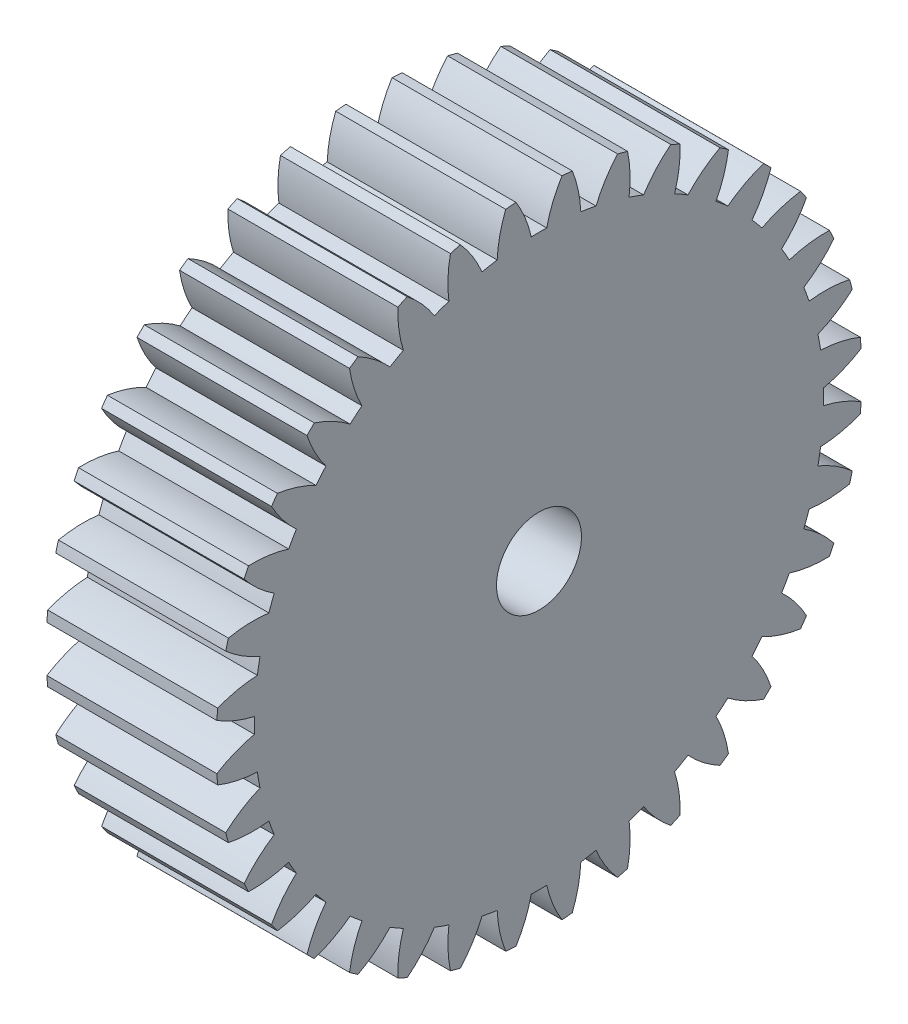
SolidWorks part; units mm, degrees
ref_plane "Plane1" through (0, 0, 0) normal (0, 0, 1) x (1, 0, 0)
ref_plane "Plane2" through (0, 0, 0) normal (0, 1, 0) x (1, 0, 0)
ref_plane "Plane3" through (0, 0, 0) normal (1, 0, 0) x (0, 0, -1)
other "Configuration Table"
sketch "HoldingSke" plane through (0, 0, 0) normal (0, 1, 0) x (1, 0, 0)
  line L0 (0, 0) -> (0.809, -0.5878)
  line L1 (-15, 0) -> (100, 0) construction
  line L2 (0, 0) -> (-2.1039, 2.3779)
  line L3 (0, 0) -> (-11.863, 4.5341)
  line L4 (0, 0) -> (6.9867, 5.0761)
  line L5 (0, 0) -> (-46.8476, -17.4728)
  line L6 (0, 0) -> (-8.2896, -5.593)
  line L7 (-2.1039, 2.3779) -> (8.6586, 51.2059)
  line L8 (-76.2, 54.61) -> (-75.3, 54.61)
  line L9 (-71.009, 38.7566) -> (-53.1078, 45.2721)
  line L10 (-76.2, 71.12) -> (104.1128, 71.12)
  line L11 (0, 0) -> (-10, 0)
  line L12 (-76.2, 101.6) -> (-76.162, 101.6)
  line L13 (24.9733, 27.94) -> (52.9518, 28.4284)
  line L14 (24.9733, 27.94) -> (24.9743, 27.94)
  line L15 (24.9733, 27.94) -> (100.4006, 29.5858)
  line L16 (-63.627, -1) -> (-12.827, -1)
  circle A0 centre (0, 0) radius 2.5
  circle A1 centre (0, 0) radius 16.749
  circle A2 centre (0, 0) radius 37.5
  circle A3 centre (0, 0) radius 2.5
  dimension "MHD" = 33.498
  dimension "Hub_dia" = 75
  dimension "Bore" = 5
  dimension "MBD" = 5
  dimension "Num_teeth" = 36
  dimension "Pitch" = 1
  dimension "Overall_len" = 50
  dimension "Show_teeth" = 36
  dimension "Thickness" = 10
  dimension "OAL" = 50.0001
  dimension "T_dim" = 0.9
  dimension "Ap" = 20
  dimension "H" = 19.05
  dimension "Pitch_radius" = 180.3128
  dimension "Width" = 10
  dimension "Backlash" = 0.038
  dimension "Addendum_fac" = 1
  dimension "Dedendum_fac" = 1.25
  dimension "Clearance_fac" = 0.25
  dimension "Dedendum_add" = 0.001
  dimension "Module" = 1
sketch "BasProSke" plane through (0, 0, 0) normal (0, 1, 0) x (1, 0, 0)
  line L0 (-10, 0) -> (60, 0) construction
  line L1 (0, 0) -> (0, 19)
  line L2 (0, 0) -> (10, 0)
  line L3 (10, 0) -> (10, 19)
  line L4 (10, 19) -> (0, 19)
  dimension "Thickness" = 10
  dimension "Diameter" = 38
revolve "Base-Revolve" add sketch "BasProSke" angle 360 about L0
sketch "TooCutSke" plane through (0, 0, 0) normal (1, 0, 0) x (0, 0, -1)
  line L1 (0, 0) -> (0, 107) construction
  line L2 (0, 0) -> (-0.8516, 17.9798) construction
  line L3 (0, 0) -> (-3.1351, 35.8344) construction
  line L4 (-0.8516, 17.9798) -> (-1.5676, 17.9172) construction
  arc A0 (0.4547, 16.7428) -> (-0.4547, 16.7428) centre (0, 0) ccw
  arc A1 (1.3689, 18.9761) -> (-1.3689, 18.9761) centre (0, 0) ccw
  circle A2 centre (0, 0) radius 18 construction
  circle A3 centre (0, 0) radius 16.9145 construction
  arc A4 (-0.4547, 16.7428) -> (-1.3689, 18.9761) centre (-7.4808, 15.1702) ccw
  arc A5 (1.3689, 18.9761) -> (0.4547, 16.7428) centre (7.4808, 15.1702) ccw
  dimension "Root_dia" = 33.498
  dimension "Overcut_dia" = 38.0508
  dimension "Pitch_dia" = 36
  dimension "Base_dia" = 33.8289
  dimension "Flank_rad" = 7.2
  dimension "Half_ang" = 5
  dimension "Half_CT" = 0.7186
extrude "ToothCut" cut sketch "TooCutSke" along normal through all
fillet "Breaks" [suppressed] radius 0.02
fillet "RootFillets" [suppressed] radius 0.251
pattern_circular "TeethCuts" count 36 every 10 about axis through (-10, 0, 0) along (1, 0, 0) of "ToothCut", "RootFillets", "Breaks"
sketch "HubNeaOneSke" plane through (0, 0, 0) normal (-1, 0, 0) x (0, 0, 1)
  circle A0 centre (0, 0) radius 16.749
  dimension "Diameter" = 33.498
extrude "HubNearOne" [suppressed] add sketch "HubNeaOneSke" along normal blind 40.0001
sketch "HubNeaBotSke" plane through (0, 0, 0) normal (-1, 0, 0) x (0, 0, 1)
  circle A0 centre (0, 0) radius 16.749
  dimension "Diameter" = 33.498
extrude "HubNearBoth" [suppressed] add sketch "HubNeaBotSke" along normal blind 20
ref_plane "FarPln" through (10, 0, 0) normal (1, 0, 0) x (0, 0, -1)
sketch "HubFarSke" plane through (10, 0, 0) normal (1, 0, 0) x (0, 0, -1)
  circle A0 centre (0, 0) radius 16.749
  dimension "Diameter" = 33.498
extrude "HubFar" [suppressed] add sketch "HubFarSke" along normal blind 20
sketch "BorSke" plane through (0, 0, 0) normal (1, 0, 0) x (0, 0, -1)
  circle A0 centre (0, 0) radius 2.5
  dimension "Diameter" = 5
extrude "Bore" cut sketch "BorSke" along normal mid plane 100.0001
sketch "KeySke" plane through (0, 0, 0) normal (1, 0, 0) x (0, 0, -1)
  line L0 (-1, 0) -> (-1, 3.4)
  line L1 (-1, 3.4) -> (1, 3.4)
  line L2 (1, 3.4) -> (1, 0)
  line L3 (0, 0) -> (0, 34) construction
  line L4 (-1, 0) -> (1, 0)
  dimension "Offset" = 3.4
  dimension "Width" = 2
extrude "Keyway" [suppressed] cut sketch "KeySke" along normal mid plane 100.0001
pattern_circular "Keyway2" [suppressed] count 2 every 90 about axis through (-10, 0, 0) along (1, 0, 0)
equation "' \"Module@HoldingSke\" = 6.35"
equation "' \"Num_teeth@HoldingSke\" = 12"
equation "' \"Ap@HoldingSke\" =  20"
equation "' \"Ap@HoldingSke\" = 20"
equation "' \"Width@HoldingSke\" = 0.5 * 25.4"
equation "' \"Hub_dia@HoldingSke\"= 1 * 25.4"
equation "' \"Hub_dia@HoldingSke\" = 1 * 25.4"
equation "' \"Overall_len@HoldingSke\" = 1.0 * 25.4"
equation "' \"Bore@HoldingSke\" = 0.75 * 25.4"
equation "' \"T_dim@HoldingSke\" = 0.1 * 25.4"
equation "' \"Width@KeySke\" = 0.25 * 25.4"
equation "' \"Show_teeth@HoldingSke\" = 13"
equation "' \"Backlash@HoldingSke\" = 0.009 * 25.4"
equation "' \"Addendum_fac@HoldingSke\" = 1.0"
equation "' \"Dedendum_fac@HoldingSke\" = 1.25"
equation "' \"Dedendum_add@HoldingSke\" = 0.00005 * 25.4"
equation "' \"Clearance_fac@HoldingSke\" = 0.25"
equation "\"Pitch@HoldingSke\" = 1 / \"Module@HoldingSke\""
equation "\"Overcut_dia@TooCutSke\" = (\"Num_teeth@HoldingSke\" + 2 * \"Addendum_fac@HoldingSke\") / \"Pitch@HoldingSke\" + 0.002 * 25.4"
equation "\"Pitch_dia@TooCutSke\" = \"Num_teeth@HoldingSke\" / \"Pitch@HoldingSke\""
equation "\"Base_dia@TooCutSke\" = \"Num_teeth@HoldingSke\" / \"Pitch@HoldingSke\" * cos((\"Ap@HoldingSke\"  * 3.14159265 / 180))"
equation "\"Root_dia@TooCutSke\" = (\"Num_teeth@HoldingSke\" + 2) / \"Pitch@HoldingSke\" - 2 * (\"Addendum_fac@HoldingSke\" + \"Dedendum_fac@HoldingSke\") / \"Pitch@HoldingSke\" - \"Dedendum_add@HoldingSke\" * 2"
equation "\"Half_ang@TooCutSke\" = 180 / \"Num_teeth@HoldingSke\""
equation "\"Half_CT@TooCutSke\" = \"Num_teeth@HoldingSke\" / \"Pitch@HoldingSke\" * sin((3.14159265 / 2 / \"Num_teeth@HoldingSke\")) / 2 - 7 * \"Backlash@HoldingSke\" / 4"
equation "\"Flank_rad@TooCutSke\" = \"Num_teeth@HoldingSke\" / \"Pitch@HoldingSke\" / 5"
equation "\"Radius@RootFillets\" = \"Clearance_fac@HoldingSke\" / \"Pitch@HoldingSke\" + \"Dedendum_add@HoldingSke\""
equation "\"Break_rad@Breaks\" = 0.02 / \"Pitch@HoldingSke\""
equation "\"Thickness@HoldingSke\" = \"Width@HoldingSke\""
equation "\"OAL@HoldingSke\" = \"Thickness@HoldingSke\""
equation "\"MHD@HoldingSke\" = (\"Num_teeth@HoldingSke\" + 2) / \"Pitch@HoldingSke\" - 2 * (\"Addendum_fac@HoldingSke\" + \"Dedendum_fac@HoldingSke\")  / \"Pitch@HoldingSke\" - \"Dedendum_add@HoldingSke\" * 2"
equation "\"MBD@HoldingSke\" = (\"Num_teeth@HoldingSke\" + 2) / \"Pitch@HoldingSke\" - 2 * (\"Addendum_fac@HoldingSke\" + \"Dedendum_fac@HoldingSke\")  / \"Pitch@HoldingSke\" - \"Dedendum_add@HoldingSke\" * 2 - 0.002 * 25.4"
equation "\"MHD@HoldingSke\" = ((sgn( \"MHD@HoldingSke\" - \"Hub_dia@HoldingSke\" )-1)*( \"MHD@HoldingSke\" - \"Hub_dia@HoldingSke\" ))/-2+ \"Hub_dia@HoldingSke\""
equation "\"MBD@HoldingSke\" = ((sgn( \"MBD@HoldingSke\" - \"Bore@HoldingSke\" )-1)*( \"MBD@HoldingSke\" - \"Bore@HoldingSke\" ))/-2+ \"Bore@HoldingSke\""
equation "\"OAL@HoldingSke\" = ((sgn( \"OAL@HoldingSke\" - \"Overall_len@HoldingSke\" )+1)*( \"OAL@HoldingSke\" - \"Overall_len@HoldingSke\" ))/2 + \"Overall_len@HoldingSke\" + 0.000002 * 25.4"
equation "\"Num_teeth@TeethCuts\" = int( \"Show_teeth@HoldingSke\" ) + 1"
equation "\"Num_teeth@TeethCuts\" = ((sgn( \"Num_teeth@TeethCuts\" - \"Num_teeth@HoldingSke\" )-1)*( \"Num_teeth@TeethCuts\" - \"Num_teeth@HoldingSke\" ))/-2+ \"Num_teeth@HoldingSke\""
equation "\"Num_teeth@TeethCuts\" = ((sgn( \"Num_teeth@TeethCuts\" - 2.0)+1)*( \"Num_teeth@TeethCuts\" - 2.0))/2 +2.0"
equation "\"Angle@TeethCuts\" = 360.0 / \"Num_teeth@HoldingSke\""
equation "\"Diameter@BasProSke\" = (\"Num_teeth@HoldingSke\" + 2 * \"Addendum_fac@HoldingSke\") / \"Pitch@HoldingSke\""
equation "\"Thickness@BasProSke\"  = \"Thickness@HoldingSke\""
equation "' \"Fillet_rad@BasProSke\" =  \"Thickness@HoldingSke\" * 0.05"
equation "' \"Fillet_rad@BasProSke\" = \"Thickness@HoldingSke\" * 0.05"
equation "\"MHD@HoldingSke\" = ((sgn( \"MHD@HoldingSke\" - \"Root_dia@TooCutSke\" )-1)*( \"MHD@HoldingSke\" - \"Root_dia@TooCutSke\" ))/-2+ \"Root_dia@TooCutSke\""
equation "\"Diameter@HubNeaOneSke\" = \"MHD@HoldingSke\""
equation "\"Length@HubNearOne\" = \"OAL@HoldingSke\" - \"Thickness@BasProSke\""
equation "\"Diameter@HubNeaBotSke\" = \"MHD@HoldingSke\""
equation "\"Length@HubNearBoth\" = ( \"OAL@HoldingSke\" - \"Thickness@BasProSke\" ) / 2.0"
equation "\"Thickness@FarPln\" = \"Thickness@BasProSke\""
equation "\"Diameter@HubFarSke\" = \"MHD@HoldingSke\""
equation "\"Length@HubFar\" = ( \"OAL@HoldingSke\" - \"Thickness@BasProSke\" ) / 2.0"
equation "\"Diameter@BorSke\" = \"MBD@HoldingSke\""
equation "\"D1@Bore\" = \"OAL@HoldingSke\" * 2.0"
equation "\"D1@Keyway\" = \"OAL@HoldingSke\" * 2.0"
equation "\"Offset@KeySke\" = \"T_dim@HoldingSke\" + \"MBD@HoldingSke\" / 2.0"
